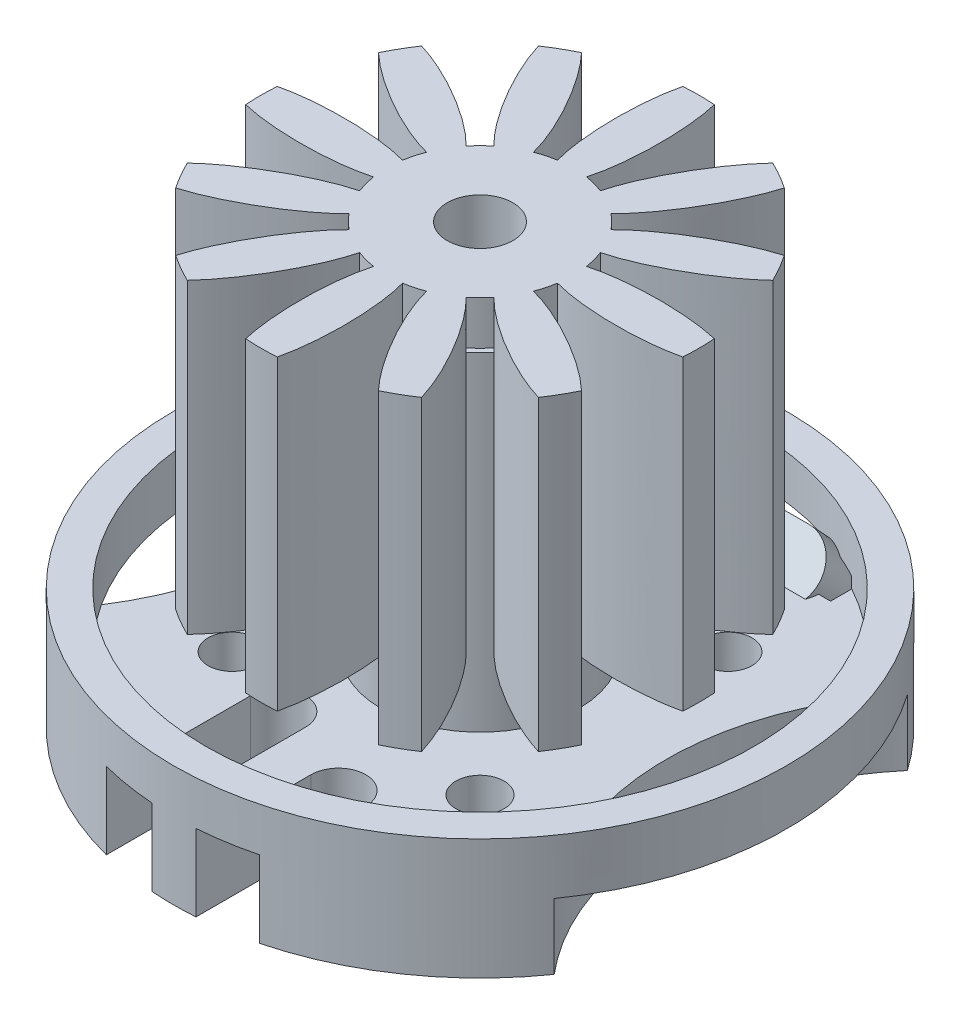
SolidWorks part; units mm, degrees
ref_plane "Front" through (0, 0, 0) normal (0, 0, 1) x (1, 0, 0)
ref_plane "Top" through (0, 0, 0) normal (0, 1, 0) x (1, 0, 0)
ref_plane "Right" through (0, 0, 0) normal (1, 0, 0) x (0, 0, -1)
sketch "Sketch1" plane through (0, 0, 0) normal (0, 1, 0) x (1, 0, 0)
  circle A0 centre (0, 0) radius 14
  dimension "D1" = 28
extrude "Base" add sketch "Sketch1" along normal blind 5.5
sketch "Sketch2" plane through (0, 5.5, 0) normal (0, 1, 0) x (1, 0, 0)
  circle A0 centre (0, 0) radius 12.5
  dimension "D1" = 25
extrude "BaseCut" cut sketch "Sketch2" against normal blind 2.5
sketch "Sketch5" plane through (0, 3, 0) normal (0, 1, 0) x (1, 0, 0)
  circle A0 centre (0, 0) radius 4.5
  dimension "D1" = 9
extrude "OuterShaft" add sketch "Sketch5" along normal blind 15
sketch "Sketch6" plane through (0, 0, 0) normal (0, -1, 0) x (-1, 0, 0)
  line L0 (14, 0) -> (-14, 0) construction
  line L1 (0, -14) -> (0, 14) construction
  circle A0 centre (-21, 0) radius 12.5
  circle A2 centre (0, 0) radius 14 construction
  circle A3 centre (21, 0) radius 12.5
  dimension "D1" = 25
  dimension "D2" = 21
extrude "LightWeight1" cut sketch "Sketch6" against normal blind 3
ref_plane "PlaneForInductors" through (0, 6, 0) normal (0, 1, 0) x (1, 0, 0)
sketch "Sketch4" plane through (0, 6, 0) normal (0, 1, 0) x (1, 0, 0)
  arc A0 (-2.6716, 3.3053) -> (-3.3053, 2.6716) centre (0, 0) ccw
  arc A1 (-9.974, 0.7204) -> (-9.974, -0.7204) centre (0, 0) ccw
  arc A2 (-8.2776, 5.6109) -> (-8.9979, 4.3632) centre (0, 0) ccw
  arc A3 (-4.3632, 8.9979) -> (-5.6109, 8.2776) centre (0, 0) ccw
  arc A4 (-0.6611, 4.1983) -> (-1.5267, 3.9663) centre (0, 0) ccw
  arc A5 (1.5267, 3.9663) -> (0.6611, 4.1983) centre (0, 0) ccw
  arc A6 (3.3053, 2.6716) -> (2.6716, 3.3053) centre (0, 0) ccw
  arc A7 (4.1983, 0.6611) -> (3.9663, 1.5267) centre (0, 0) ccw
  arc A8 (3.9663, -1.5267) -> (4.1983, -0.6611) centre (0, 0) ccw
  arc A9 (2.6716, -3.3053) -> (3.3053, -2.6716) centre (0, 0) ccw
  arc A10 (0.6611, -4.1983) -> (1.5267, -3.9663) centre (0, 0) ccw
  arc A11 (-1.5267, -3.9663) -> (-0.6611, -4.1983) centre (0, 0) ccw
  arc A12 (-3.3053, -2.6716) -> (-2.6716, -3.3053) centre (0, 0) ccw
  arc A13 (-4.1983, -0.6611) -> (-3.9663, -1.5267) centre (0, 0) ccw
  arc A14 (-3.9663, 1.5267) -> (-4.1983, 0.6611) centre (0, 0) ccw
  arc A15 (0.7204, 9.974) -> (-0.7204, 9.974) centre (0, 0) ccw
  arc A16 (5.6109, 8.2776) -> (4.3632, 8.9979) centre (0, 0) ccw
  arc A17 (8.9979, 4.3632) -> (8.2776, 5.6109) centre (0, 0) ccw
  arc A18 (9.974, -0.7204) -> (9.974, 0.7204) centre (0, 0) ccw
  arc A19 (8.2776, -5.6109) -> (8.9979, -4.3632) centre (0, 0) ccw
  arc A20 (4.3632, -8.9979) -> (5.6109, -8.2776) centre (0, 0) ccw
  arc A21 (-0.7204, -9.974) -> (0.7204, -9.974) centre (0, 0) ccw
  arc A22 (-5.6109, -8.2776) -> (-4.3632, -8.9979) centre (0, 0) ccw
  arc A23 (-8.9979, -4.3632) -> (-8.2776, -5.6109) centre (0, 0) ccw
  ellipse E0 centre (-7.1996, 0) end of major axis (-11.1996, 0) minor radius 1 (-9.974, -0.7204) -> (-4.1983, -0.6611) ccw
  ellipse E1 centre (-7.1996, 0) end of major axis (-11.1996, 0) minor radius 1 (-4.1983, 0.6611) -> (-9.974, 0.7204) ccw
  ellipse E2 centre (-6.2351, 3.5998) end of major axis (-2.771, 1.5998) minor radius 1 (-3.3053, 2.6716) -> (-8.2776, 5.6109) ccw
  ellipse E3 centre (-6.2351, 3.5998) end of major axis (-2.771, 1.5998) minor radius 1 (-8.9979, 4.3632) -> (-3.9663, 1.5267) ccw
  ellipse E4 centre (-3.5998, 6.2351) end of major axis (-5.5998, 9.6992) minor radius 1 (-1.5267, 3.9663) -> (-4.3632, 8.9979) ccw
  ellipse E5 centre (-3.5998, 6.2351) end of major axis (-5.5998, 9.6992) minor radius 1 (-5.6109, 8.2776) -> (-2.6716, 3.3053) ccw
  ellipse E6 centre (0, 7.1996) end of major axis (0, 3.1996) minor radius 1 (0.6611, 4.1983) -> (0.7204, 9.974) ccw
  ellipse E7 centre (0, 7.1996) end of major axis (0, 11.1996) minor radius 1 (-0.7204, 9.974) -> (-0.6611, 4.1983) ccw
  ellipse E8 centre (3.5998, 6.2351) end of major axis (5.5998, 9.6992) minor radius 1 (2.6716, 3.3053) -> (5.6109, 8.2776) ccw
  ellipse E9 centre (3.5998, 6.2351) end of major axis (5.5998, 9.6992) minor radius 1 (4.3632, 8.9979) -> (1.5267, 3.9663) ccw
  ellipse E10 centre (6.2351, 3.5998) end of major axis (9.6992, 5.5998) minor radius 1 (3.9663, 1.5267) -> (8.9979, 4.3632) ccw
  ellipse E11 centre (6.2351, 3.5998) end of major axis (2.771, 1.5998) minor radius 1 (8.2776, 5.6109) -> (3.3053, 2.6716) ccw
  ellipse E12 centre (7.1996, 0) end of major axis (11.1996, 0) minor radius 1 (4.1983, -0.6611) -> (9.974, -0.7204) ccw
  ellipse E13 centre (7.1996, 0) end of major axis (11.1996, 0) minor radius 1 (9.974, 0.7204) -> (4.1983, 0.6611) ccw
  ellipse E14 centre (6.2351, -3.5998) end of major axis (9.6992, -5.5998) minor radius 1 (3.3053, -2.6716) -> (8.2776, -5.6109) ccw
  ellipse E15 centre (6.2351, -3.5998) end of major axis (9.6992, -5.5998) minor radius 1 (8.9979, -4.3632) -> (3.9663, -1.5267) ccw
  ellipse E16 centre (3.5998, -6.2351) end of major axis (1.5998, -2.771) minor radius 1 (1.5267, -3.9663) -> (4.3632, -8.9979) ccw
  ellipse E17 centre (3.5998, -6.2351) end of major axis (5.5998, -9.6992) minor radius 1 (5.6109, -8.2776) -> (2.6716, -3.3053) ccw
  ellipse E18 centre (0, -7.1996) end of major axis (0, -11.1996) minor radius 1 (-0.6611, -4.1983) -> (-0.7204, -9.974) ccw
  ellipse E19 centre (0, -7.1996) end of major axis (0, -11.1996) minor radius 1 (0.7204, -9.974) -> (0.6611, -4.1983) ccw
  ellipse E20 centre (-3.5998, -6.2351) end of major axis (-5.5998, -9.6992) minor radius 1 (-2.6716, -3.3053) -> (-5.6109, -8.2776) ccw
  ellipse E21 centre (-3.5998, -6.2351) end of major axis (-5.5998, -9.6992) minor radius 1 (-4.3632, -8.9979) -> (-1.5267, -3.9663) ccw
  ellipse E22 centre (-6.2351, -3.5998) end of major axis (-9.6992, -5.5998) minor radius 1 (-3.9663, -1.5267) -> (-8.9979, -4.3632) ccw
  ellipse E23 centre (-6.2351, -3.5998) end of major axis (-2.771, -1.5998) minor radius 1 (-8.2776, -5.6109) -> (-3.3053, -2.6716) ccw
  point P163 (0, 0)
  dimension "D1" = 20
  dimension "D2" = 8.5
  dimension "D3" = 2
  dimension "D4" = 8
extrude "Inductors" add sketch "Sketch4" along normal blind 14
sketch "Sketch7" plane through (0, 0, 0) normal (0, -1, 0) x (1, 0, 0)
  line L0 (-3.5, 13.9642) -> (-3.5, 6.9642)
  line L1 (-1, 10.4642) -> (1, 10.4642) construction
  line L2 (-6, -10) -> (6, -10)
  line L3 (-6, -10) -> (-6, -18)
  line L4 (-6, -18) -> (6, -18)
  line L5 (6, -10) -> (6, -18)
  line L6 (-1, 6.9642) -> (-1, 13.9642)
  line L7 (-1, 13.9642) -> (-3.5, 13.9642)
  line L8 (1, 13.9642) -> (1, 8.7142)
  line L9 (-6, -10) -> (6, -18) construction
  line L10 (3.5, 8.7142) -> (3.5, 13.9642)
  line L11 (3.5, 13.9642) -> (1, 13.9642)
  line L12 (-6, -18) -> (6, -10) construction
  arc A0 (-3.5, 6.9642) -> (-1, 6.9642) centre (-2.25, 6.9642) ccw
  arc A1 (1, 8.7142) -> (3.5, 8.7142) centre (2.25, 8.7142) ccw
  arc A2 (-11.4464, -8.061) -> (11.4464, -8.061) centre (0, 0) ccw construction
  arc A3 (11.4464, 8.061) -> (-11.4464, 8.061) centre (0, 0) ccw construction
  point P0 (0, -14)
  point P24 (0, 10.4642)
  dimension "D4" = 5.25
  dimension "D1" = 2
  dimension "D2" = 12
  dimension "D3" = 8
  dimension "D7" = 2.5
  dimension "D8" = 7
extrude "LighWeigth2" cut sketch "Sketch7" against normal blind 3.5
sketch "Sketch8" plane through (0, 0, 0) normal (0, -1, 0) x (-1, 0, 0)
  circle A0 centre (0, 0) radius 3.75
  dimension "D1" = 7.5
extrude "LightWeightForShaft" cut sketch "Sketch8" against normal blind 0.5
sketch "Sketch9" plane through (0, 0.5, 0) normal (0, -1, 0) x (-1, 0, 0)
  circle A0 centre (0, 0) radius 1.5
  dimension "D1" = 3
extrude "HoleForShaft" cut sketch "Sketch9" against normal through all
hole_wizard "Ø2.0 ScrewHoles" positions "Sketch11" profile "Sketch10" hole size "Ø2.2" standard "ANSI Metric"
sketch "Sketch11" plane through (0, 0, 0) normal (0, -1, 0) x (-1, 0, 0)
  line L0 (0, 0) -> (-9.8995, 9.8995) construction
  line L2 (0, 0) -> (0, 14) construction
  arc A4 (-6, 12.6491) -> (-11.4464, 8.061) centre (0, 0) ccw construction
  arc A5 (6, 12.6491) -> (-6, 12.6491) centre (0, 0) ccw construction
  point P30 (-1.9171, -4.8513)
  point P49 (-5.6569, 5.6569)
  point P70 (5.6569, 5.6569)
  point P71 (5.6569, -5.6569)
  point P72 (-5.6569, -5.6569)
  point P73 (0, 0)
  dimension "D1" = 8
  dimension "D2" = 45
  dimension "D3" = 4
sketch "Sketch10" plane through (5.6569, 0, -5.6569) normal (1, 0, 0) x (0, 0, -1)
  line L0 (0, 0) -> (0, 4.6609)
  line L1 (0, 4.6609) -> (1.1, 4)
  line L2 (1.1, 4) -> (1.1, 0)
  line L5 (1.1, 0) -> (0, 0)
  line L10 (0, 4.6609) -> (-1.1, 4) construction
  line L11 (0, -6.35) -> (0, 107.95) construction
  dimension "Hole Dia." = 2.2
  dimension "Hole Depth" = 4
  dimension "Drill Angle" = 118
ref_plane "PlaneForCables" through (0, -3.25, -3.25) normal (0, -0.7071, -0.7071) x (-1, 0, 0)
sketch "Sketch12" plane through (0, -3.25, -3.25) normal (0, -0.7071, -0.7071) x (-1, 0, 0)
  line L0 (-4, 9.4924) -> (4, 9.4924) construction
  line L1 (-4, 10.9924) -> (4, 10.9924)
  line L2 (-4, 7.9924) -> (4, 7.9924)
  line L3 (6, 9.1924) -> (-6, 9.1924) construction
  arc A0 (-4, 10.9924) -> (-4, 7.9924) centre (-4, 9.4924) ccw
  arc A1 (4, 7.9924) -> (4, 10.9924) centre (4, 9.4924) ccw
  point P2 (0, 9.4924)
  dimension "D3" = 8
  dimension "D1" = 3
  dimension "D2" = 0.3
extrude "cableOut" add sketch "Sketch12" along normal blind 5 draft 2
sketch "Sketch13" plane through (0, -6.7855, -6.7855) normal (0, -0.7071, -0.7071) x (-1, 0, 0)
  line L0 (-5.3254, 9.4924) -> (5.3254, 9.4924) construction
  line L1 (0, 10.8178) -> (0, 8.167) construction
  line L2 (4, 10.8178) -> (-4, 10.8178) construction
  line L3 (-4, 8.167) -> (4, 8.167) construction
  circle A0 centre (-2.1, 9.4924) radius 1
  arc A1 (-4, 10.8178) -> (-4, 8.167) centre (-4, 9.4924) ccw construction
  arc A2 (4, 8.167) -> (4, 10.8178) centre (4, 9.4924) ccw construction
  circle A3 centre (0, 9.4924) radius 1
  circle A4 centre (2.1, 9.4924) radius 1
  dimension "D1" = 2
  dimension "D3" = 2.1
  dimension "D2" = 3
extrude "Boss-Extrude2" add sketch "Sketch13" along normal blind 2
equation "\"LightWeightLength\"= 7"
equation "\"LightWeightLengthShort\"= \"LightWeightLength\" * 0.75'den lilla"
equation "\"D8@Sketch7\"=\"LightWeightLength\""
equation "\"D4@Sketch7\"=\"LightWeightLengthShort\""
